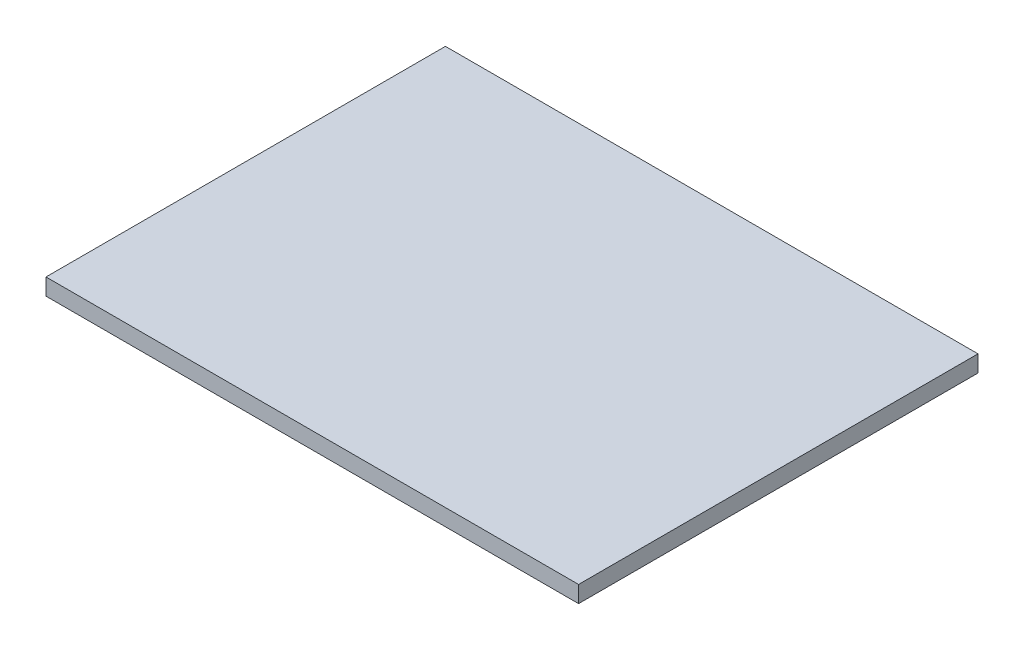
SolidWorks part; units mm, degrees
ref_plane "Front Plane" through (0, 0, 0) normal (0, 0, 1) x (1, 0, 0)
ref_plane "Top Plane" through (0, 0, 0) normal (0, 1, 0) x (1, 0, 0)
ref_plane "Right Plane" through (0, 0, 0) normal (1, 0, 0) x (0, 0, -1)
sketch "Sketch1" plane through (0, 0, 0) normal (0, 1, 0) x (1, 0, 0)
  line L1 (-203.2, 152.4) -> (203.2, 152.4)
  line L2 (-203.2, 152.4) -> (-203.2, -152.4)
  line L3 (-203.2, -152.4) -> (203.2, -152.4)
  line L4 (203.2, 152.4) -> (203.2, -152.4)
  line L5 (-203.2, 152.4) -> (203.2, -152.4) construction
  line L6 (-203.2, -152.4) -> (203.2, 152.4) construction
  point P0 (0, 0)
  dimension "D1" = 406.4
  dimension "D2" = 304.8
extrude "Boss-Extrude1" add sketch "Sketch1" along normal blind 12.7
